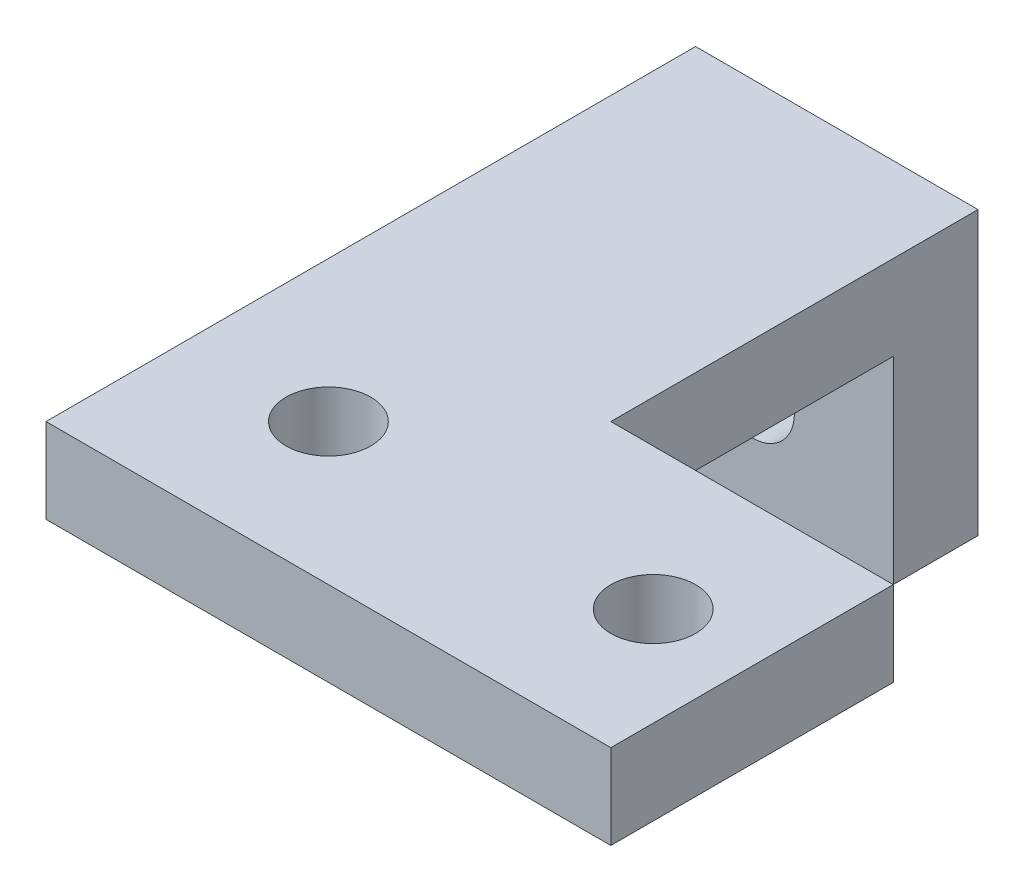
SolidWorks part; units mm, degrees
ref_plane "Front Plane" through (0, 0, 0) normal (0, 0, 1) x (1, 0, 0)
ref_plane "Top Plane" through (0, 0, 0) normal (0, 1, 0) x (1, 0, 0)
ref_plane "Right Plane" through (0, 0, 0) normal (1, 0, 0) x (0, 0, -1)
sketch "Sketch1" plane through (0, 0, 0) normal (0, 1, 0) x (1, 0, 0)
  line L0 (0, 0) -> (0, 10)
  line L1 (0, 10) -> (-10, 10)
  line L2 (-10, 10) -> (-10, -10)
  line L3 (-10, -10) -> (10, -10)
  line L4 (10, -10) -> (10, 0)
  line L5 (10, 0) -> (0, 0)
  dimension "D1" = 20
  dimension "D2" = 20
  dimension "D3" = 10
  dimension "D4" = 10
extrude "Boss-Extrude1" add sketch "Sketch1" along normal blind 3
sketch "Sketch2" plane through (0, 3, 0) normal (0, 1, 0) x (1, 0, 0)
  line L1 (0, 10) -> (-10, 10)
  line L2 (0, 10) -> (0, 13)
  line L3 (0, 13) -> (-10, 13)
  line L4 (-10, 10) -> (-10, 13)
  dimension "D1" = 3
extrude "Boss-Extrude2" add sketch "Sketch2" against normal blind 10
sketch "Sketch3" plane through (0, 3, 0) normal (0, 1, 0) x (1, 0, 0)
  line L0 (-10, -10) -> (10, -10) construction
  circle A0 centre (-5, -5) radius 1.5
  circle A1 centre (6.5, -5) radius 1.5
  dimension "D1" = 3
  dimension "D2" = 3
  dimension "D3" = 5
  dimension "D4" = 5
  dimension "D5" = 5
  dimension "D6" = 3.5
extrude "Cut-Extrude1" cut sketch "Sketch3" against normal up to next
sketch "Sketch4" plane through (0, 0, -13) normal (0, 0, -1) x (-1, 0, 0)
  line L0 (0, -7) -> (10, -7) construction
  circle A0 centre (5, -3.5) radius 1.5
  dimension "D1" = 3
  dimension "D2" = 5
  dimension "D3" = 3.5
extrude "Cut-Extrude2" cut sketch "Sketch4" against normal up to next
